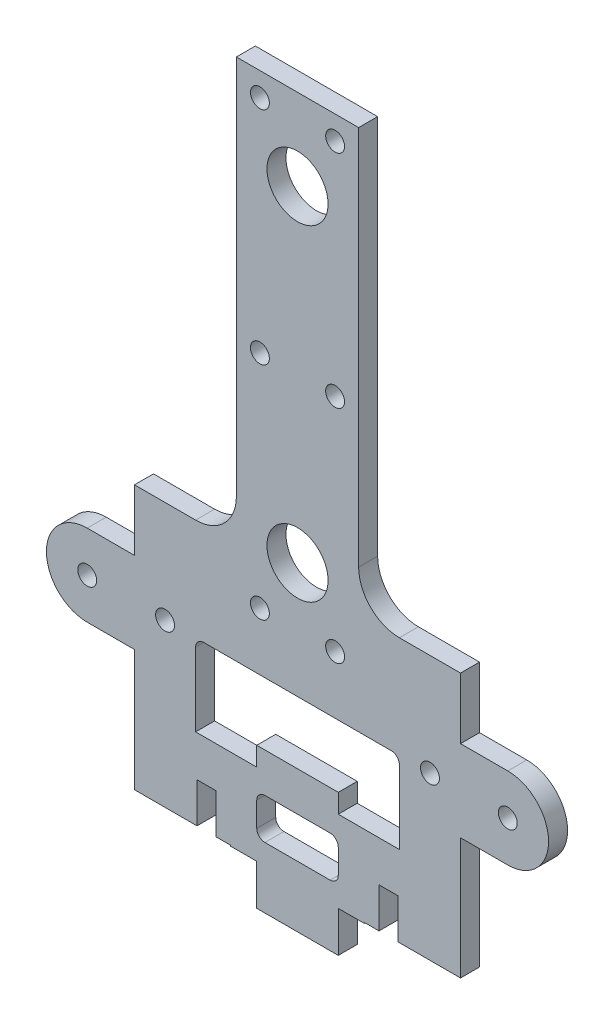
SolidWorks part; units mm, degrees
ref_plane "Front Plane" through (0, 0, 0) normal (0, 0, 1) x (1, 0, 0)
ref_plane "Top Plane" through (0, 0, 0) normal (0, 1, 0) x (1, 0, 0)
ref_plane "Right Plane" through (0, 0, 0) normal (1, 0, 0) x (0, 0, -1)
sketch "Sketch1" plane through (0, 0, 0) normal (0, 0, 1) x (1, 0, 0)
  line L0 (0, 17.6683) -> (0, -48.4482) construction
  line L1 (-15.875, -12.7) -> (-15.875, -25.4) construction
  line L2 (6.35, -25.4) -> (6.35, -31.75)
  line L3 (6.35, -25.4) -> (25.4, -25.4)
  line L4 (25.4, -25.4) -> (25.4, -6.35)
  line L5 (-15.875, -19.05) -> (12.3134, -19.05) construction
  line L6 (6.35, -9.7409) -> (-6.35, -9.7409)
  line L7 (32.766, -6.35) -> (25.4, -6.35)
  line L8 (32.766, 6.35) -> (15.875, 6.35)
  line L9 (-32.766, -6.35) -> (-25.4, -6.35)
  line L10 (6.35, -31.75) -> (-6.35, -31.75)
  line L11 (-25.4, -25.4) -> (-25.4, -6.35)
  line L12 (-6.35, -25.4) -> (-25.4, -25.4)
  line L13 (-6.35, -25.4) -> (-6.35, -31.75)
  line L14 (6.35, -12.7) -> (6.35, -9.7409)
  line L15 (-15.875, 6.35) -> (-32.766, 6.35)
  line L16 (-6.35, -12.7) -> (-6.35, -9.7409)
  line L17 (-15.875, 6.35) -> (-15.875, -12.7)
  line L18 (-15.875, -12.7) -> (-6.35, -12.7)
  line L19 (15.875, 6.35) -> (15.875, -12.7)
  line L20 (6.35, -12.7) -> (15.875, -12.7)
  line L22 (-5.08, -15.875) -> (5.08, -15.875)
  line L23 (-6.35, -17.145) -> (-6.35, -20.955)
  line L24 (-5.08, -22.225) -> (5.08, -22.225)
  line L25 (6.35, -17.145) -> (6.35, -20.955)
  line L26 (-6.35, -15.875) -> (6.35, -22.225) construction
  line L27 (-6.35, -22.225) -> (6.35, -15.875) construction
  circle A0 centre (32.766, 0) radius 1.4732
  arc A1 (32.766, -6.35) -> (32.766, 6.35) centre (32.766, 0) ccw
  arc A2 (-32.766, -6.35) -> (-32.766, 6.35) centre (-32.766, 0) cw
  circle A3 centre (-32.766, 0) radius 1.4732
  arc A4 (-6.35, -20.955) -> (-5.08, -22.225) centre (-5.08, -20.955) ccw
  arc A5 (5.08, -22.225) -> (6.35, -20.955) centre (5.08, -20.955) ccw
  arc A6 (5.08, -15.875) -> (6.35, -17.145) centre (5.08, -17.145) cw
  arc A7 (-5.08, -15.875) -> (-6.35, -17.145) centre (-5.08, -17.145) ccw
  point P29 (0, -19.05)
  dimension "D1" = 2.9464
  dimension "D7" = 12.7
  dimension "D13" = 1.27
  dimension "D2" = 65.532
  dimension "D3" = 31.75
  dimension "D4" = 12.7
  dimension "D5" = 25.4
  dimension "D6" = 12.7
  dimension "D8" = 6.35
  dimension "D9" = 9.525
  dimension "D10" = 2.9591
  dimension "D11" = 6.35
  dimension "D12" = 12.7
extrude "Boss-Extrude1" add sketch "Sketch1" along normal blind 2.9591
fillet "Fillet1" [suppressed] radius 1.27
sketch "Sketch3" [suppressed] plane through (0, 0, 2.9591) normal (0, 0, 1) x (1, 0, 0)
  line L0 (-6.35, -12.7) -> (-15.875, -12.7) construction
  line L1 (12.7, -12.7) -> (15.6591, -12.7)
  line L2 (12.7, -12.7) -> (12.7, -19.05)
  line L3 (12.7, -19.05) -> (15.6591, -19.05)
  line L4 (15.6591, -12.7) -> (15.6591, -19.05)
  line L5 (14.1796, -12.7) -> (14.1796, -25.4) construction
  line L6 (6.35, -25.4) -> (25.4, -25.4) construction
  line L7 (0, 0) -> (0, -35.4288) construction
  point P10 (14.1796, -19.05)
  dimension "D1" = 2.9591
  dimension "D2" = 25.4
extrude "Cut-Extrude1" [suppressed] cut sketch "Sketch3" against normal up to next
mirror "Mirror1" [suppressed] about plane through (0, 0, 0) normal (1, 0, 0)
sketch "Sketch4" plane through (0, 0, 2.9591) normal (0, 0, 1) x (1, 0, 0)
  line L0 (0, 0) -> (0, -29.874) construction
  line L2 (12.7, -25.4) -> (15.6591, -25.4)
  line L3 (12.7, -25.4) -> (12.7, -19.05)
  line L4 (12.7, -19.05) -> (15.6591, -19.05)
  line L5 (15.6591, -25.4) -> (15.6591, -19.05)
  line L6 (14.1795, -25.4) -> (14.1795, -12.7) construction
  line L7 (-6.35, -12.7) -> (-15.875, -12.7) construction
  point P13 (14.1795, -19.05)
  dimension "D1" = 2.9591
  dimension "D2" = 25.4
  dimension "D3" = 6.35
extrude "Cut-Extrude2" cut sketch "Sketch4" against normal up to next (2.9591 mm away)
mirror "Mirror2" about plane through (0, 0, 0) normal (1, 0, 0) of "Cut-Extrude2"
sketch "Sketch5" [suppressed] plane through (0, 0, 2.9591) normal (0, 0, 1) x (1, 0, 0)
  line L0 (-25.4, -6.5797) -> (-15.875, -6.5797) construction
  line L3 (-25.4, -6.35) -> (-25.4, -25.4) construction
  line L4 (-15.875, -12.7) -> (-15.875, 6.35) construction
  line L5 (0, 0) -> (0, -6.35) construction
  line L6 (-20.6375, -12.7) -> (-20.6375, 0) construction
  circle A0 centre (-20.6375, 0) radius 1.9812
  circle A1 centre (-20.6375, -12.7) radius 1.9812
  circle A2 centre (20.6375, -12.7) radius 1.9812
  circle A3 centre (20.6375, 0) radius 1.9812
  point P10 (-20.6375, -6.5797)
  dimension "D1" = 3.9624
  dimension "D2" = 12.7
hole_wizard "Tap Drill for #4 Helicoil1" [suppressed] positions "Sketch7" profile "Sketch6" hole size "#4-40" standard "ANSI Inch"
sketch "Sketch7" plane through (0, 0, 3.175) normal (0, 0, 1) x (1, 0, 0)
  point P0 (-19.8437, 0)
  point P3 (-19.8437, -12.7)
  point P6 (19.8437, -12.7)
  point P9 (19.8437, 0)
sketch "Sketch6" plane through (-19.8437, 0, 3.175) normal (1, 0, 0) x (0, -1, 0)
  line L0 (0, 0) -> (0, 3.175)
  line L1 (0, 3.175) -> (1.9812, 3.175)
  line L2 (1.9812, 3.175) -> (1.9812, 0)
  line L5 (1.9812, 0) -> (0, 0)
  line L11 (0, -6.35) -> (0, 107.95) construction
  dimension "Thru Hole Dia." = 3.9624
  dimension "Thru Hole Depth" = 3.175
sketch "Sketch10" plane through (0, 0, 0) normal (0, 0, -1) x (-1, 0, 0)
  line L0 (199.712, -19.9807) -> (-0.9922, 11.7693) construction
  line L1 (15.875, 6.35) -> (32.766, 6.35) construction
  line L2 (25.4, 6.35) -> (15.875, 6.35)
  line L3 (25.4, 6.35) -> (25.4, 15.875)
  line L4 (9.525, 81.5413) -> (-9.525, 81.5413)
  line L5 (-25.4, 6.35) -> (-25.4, 15.875)
  line L6 (-32.766, 6.35) -> (-15.875, 6.35) construction
  line L7 (-25.4, -25.4) -> (-25.4, -6.35) construction
  line L8 (25.4, -6.35) -> (25.4, -25.4) construction
  line L9 (0, 68.8413) -> (0, 18.0413) construction
  line L10 (-25.4, 15.875) -> (-9.525, 15.875)
  line L11 (-9.525, 81.5413) -> (-9.525, 15.875)
  line L12 (25.4, 15.875) -> (9.525, 15.875)
  line L13 (9.525, 81.5413) -> (9.525, 15.875)
  line L14 (-15.875, 6.35) -> (-15.875, 0)
  line L15 (-15.875, 6.35) -> (-15.875, -12.7) construction
  line L16 (-15.875, 0) -> (15.875, 0)
  line L17 (15.875, -12.7) -> (15.875, 6.35) construction
  line L18 (15.875, 0) -> (15.875, 6.35)
  line L19 (-15.875, 6.35) -> (-25.4, 6.35)
  circle A0 centre (0, 18.0413) radius 3.175 construction
  circle A1 centre (0, 18.0413) radius 6.35 construction
  arc A2 (32.766, -6.35) -> (32.766, 6.35) centre (32.766, 0) ccw construction
  circle A3 centre (0, 68.8413) radius 3.175 construction
  circle A4 centre (0, 68.8413) radius 6.35 construction
  dimension "D1" = 6.35
  dimension "D2" = 3.175
  dimension "D5" = 6.35
  dimension "D6" = 3.175
  dimension "D3" = 203.2
  dimension "D4" = 31.75
  dimension "D7" = 50.8
  dimension "D8" = 12.7
  dimension "D9" = 9.525
  dimension "D10" = 9.525
extrude "Boss-Extrude5" add sketch "Sketch10" against normal up to surface (2.9591 mm away) up to face at (0, -19.05, 2.9591)
fillet "Fillet2" radius 1.27 2 edges at (-15.875, 0, 1.4796) (15.875, 0, 1.4796)
fillet "Fillet3" radius 6.35 2 edges at (9.525, 15.875, 1.4796) (-9.525, 15.875, 1.4796)
hole_wizard "3/8 (0.375) Diameter Hole1" positions "Sketch16" profile "Sketch15" hole size "3/8" standard "ANSI Inch"
sketch "Sketch16" plane through (0, 0, 2.9591) normal (0, 0, 1) x (1, 0, 0)
  point P0 (0, 68.8413)
  point P3 (0, 18.0413)
sketch "Sketch15" plane through (0, 68.8413, 2.9591) normal (1, 0, 0) x (0, -1, 0)
  line L0 (0, 0) -> (0, 9.2116)
  line L1 (0, 9.2116) -> (4.7625, 6.35)
  line L2 (4.7625, 6.35) -> (4.7625, 0)
  line L5 (4.7625, 0) -> (0, 0)
  line L10 (0, 9.2116) -> (-4.7625, 6.35) construction
  line L11 (0, -6.35) -> (0, 107.95) construction
  dimension "Hole Dia." = 9.525
  dimension "Hole Depth" = 6.35
  dimension "Drill Angle" = 118
sketch "Sketch12" plane through (0, 0, 2.9591) normal (0, 0, 1) x (1, 0, 0)
  line L0 (-15.875, 15.875) -> (-25.4, 15.875) construction
  line L1 (-19.9007, 9.0338) -> (-18.0677, 12.2088)
  line L2 (-18.0677, 12.2088) -> (-19.9007, 15.3838)
  line L3 (-19.9007, 15.3838) -> (-23.5669, 15.3838)
  line L4 (-23.5669, 15.3838) -> (-25.4, 12.2088)
  line L5 (-25.4, 12.2088) -> (-23.5669, 9.0338)
  line L6 (-23.5669, 9.0338) -> (-19.9007, 9.0338)
  line L7 (-25.4, 15.875) -> (-25.4, 6.35) construction
  line L8 (-9.525, 81.5413) -> (-9.525, 22.225) construction
  line L9 (9.525, 81.5413) -> (-9.525, 81.5413) construction
  line L11 (0, 68.8413) -> (0, 18.0413) construction
  circle A0 centre (-21.7338, 12.2088) radius 3.175 construction
  circle A1 centre (-21.7338, 12.2088) radius 3.6662
  circle A2 centre (-5.8588, 77.8751) radius 3.6662
  circle A3 centre (-5.8588, 43.4413) radius 3.6662
  circle A4 centre (-5.8588, 9.0065) radius 3.6662
  circle A5 centre (5.8588, 9.0065) radius 3.6662
  circle A6 centre (5.8588, 43.4413) radius 3.6662
  circle A7 centre (5.8588, 77.8751) radius 3.6662
  point P30 (0, 43.4413)
  dimension "D1" = 6.35
  dimension "D2" = 9.0348
hole_wizard "#4 Clearance Hole1" positions "Sketch18" profile "Sketch17" hole size "#4" standard "ANSI Inch"
sketch "Sketch18" plane through (0, 0, 2.9591) normal (0, 0, 1) x (1, 0, 0)
  point P0 (-5.8588, 77.8751)
  point P3 (-5.8588, 43.4413)
  point P6 (-5.8588, 9.0065)
  point P9 (5.8588, 9.0065)
  point P12 (5.8588, 43.4413)
  point P15 (5.8588, 77.8751)
sketch "Sketch17" plane through (-5.8588, 77.8751, 2.9591) normal (1, 0, 0) x (0, -1, 0)
  line L0 (0, 0) -> (0, 7.2352)
  line L1 (0, 7.2352) -> (1.4732, 6.35)
  line L2 (1.4732, 6.35) -> (1.4732, 0)
  line L5 (1.4732, 0) -> (0, 0)
  line L10 (0, 7.2352) -> (-1.4732, 6.35) construction
  line L11 (0, -6.35) -> (0, 107.95) construction
  dimension "Hole Dia." = 2.9464
  dimension "Hole Depth" = 6.35
  dimension "Drill Angle" = 118
hole_wizard "#4 Clearance Hole2" positions "Sketch20" profile "Sketch19" hole size "#4" standard "ANSI Inch"
sketch "Sketch20" plane through (0, 0, 2.9591) normal (0, 0, 1) x (1, 0, 0)
  line L1 (-20.6375, 3.6662) -> (-23.8125, 1.8331)
  line L2 (-23.8125, 1.8331) -> (-23.8125, -1.8331)
  line L3 (-23.8125, -1.8331) -> (-20.6375, -3.6662)
  line L4 (-20.6375, -3.6662) -> (-17.4625, -1.8331)
  line L5 (-17.4625, -1.8331) -> (-17.4625, 1.8331)
  line L6 (-17.4625, 1.8331) -> (-20.6375, 3.6662)
  line L7 (-25.4, -6.35) -> (-15.875, -6.35) construction
  line L8 (-25.4, -6.35) -> (-25.4, -25.4) construction
  line L9 (-15.875, -12.7) -> (-15.875, -1.27) construction
  line L11 (0, 0) -> (0, -4.7314) construction
  circle A0 centre (-20.6375, 0) radius 3.175 construction
  point P0 (-20.6375, 0)
  point P23 (-20.6375, -6.35)
  point P32 (20.6375, 0)
  dimension "D1" = 6.35
sketch "Sketch19" plane through (-20.6375, 0, 2.9591) normal (1, 0, 0) x (0, -1, 0)
  line L0 (0, 0) -> (0, 4.1872)
  line L1 (0, 4.1872) -> (1.4732, 3.302)
  line L2 (1.4732, 3.302) -> (1.4732, 0)
  line L5 (1.4732, 0) -> (0, 0)
  line L10 (0, 4.1872) -> (-1.4732, 3.302) construction
  line L11 (0, -6.35) -> (0, 107.95) construction
  dimension "Hole Dia." = 2.9464
  dimension "Hole Depth" = 3.302
  dimension "Drill Angle" = 118
sketch "Sketch21" [suppressed] plane through (0, 0, 2.9591) normal (0, 0, 1) x (1, 0, 0)
  circle A0 centre (-15.6591, -19.05) radius 0.635
  circle A1 centre (-12.7, -19.05) radius 0.635
  circle A2 centre (12.7, -19.05) radius 0.635
  circle A3 centre (15.6591, -19.05) radius 0.635
  dimension "D1" = 1.27
extrude "Cut-Extrude3" [suppressed] cut sketch "Sketch21" against normal up to next
sketch "Sketch22" plane through (0, -25.4, 0) normal (0, -1, 0) x (1, 0, 0)
  line L0 (6.35, 2.9591) -> (12.7, 2.9591) construction
  circle A0 centre (0, -12.9159) radius 19.05
  dimension "D2" = 38.1
  dimension "D1" = 15.875
sketch "Sketch23" plane through (0, 0, 2.9591) normal (0, 0, 1) x (1, 0, 0)
  line L0 (-19.05, -25.4) -> (19.05, -25.4) construction
  line L1 (-25.4, -25.4) -> (-15.6591, -25.4) construction
  line L2 (6.35, -25.4) -> (12.7, -25.4) construction
  line L3 (-10.4033, -25.273) -> (-10.4033, -25.4)
  line L4 (-10.4033, -25.273) -> (-25.4, -25.273)
  line L5 (-25.4, -6.35) -> (-25.4, -25.4) construction
  line L6 (-25.4, -25.273) -> (-25.4, -25.4)
  line L7 (-10.4033, -25.4) -> (-25.4, -25.4)
  point P0 (-10.5303, -25.4)
  point P1 (10.5303, -25.4)
  dimension "D1" = 0.127
  dimension "D2" = 0.127
extrude "Cut-Extrude4" cut sketch "Sketch23" against normal up to next (2.9591 mm away)
mirror "Mirror3" about plane through (0, 0, 0) normal (1, 0, 0) of "Cut-Extrude4"
sketch "Sketch24" [suppressed] plane through (0, 0, 0) normal (0, 0, -1) x (-1, 0, 0)
  line L1 (-15.6591, -12.7) -> (-15.875, -12.7)
  line L2 (-15.6591, -12.7) -> (-15.6591, 6.35)
  line L3 (-15.6591, 6.35) -> (-15.875, 6.35)
  line L4 (-15.875, -12.7) -> (-15.875, 6.35)
extrude "Boss-Extrude6" [suppressed] add sketch "Sketch24" against normal up to surface (2.9591 mm away)
mirror "Mirror4" [suppressed] about plane through (0, 0, 0) normal (1, 0, 0)
